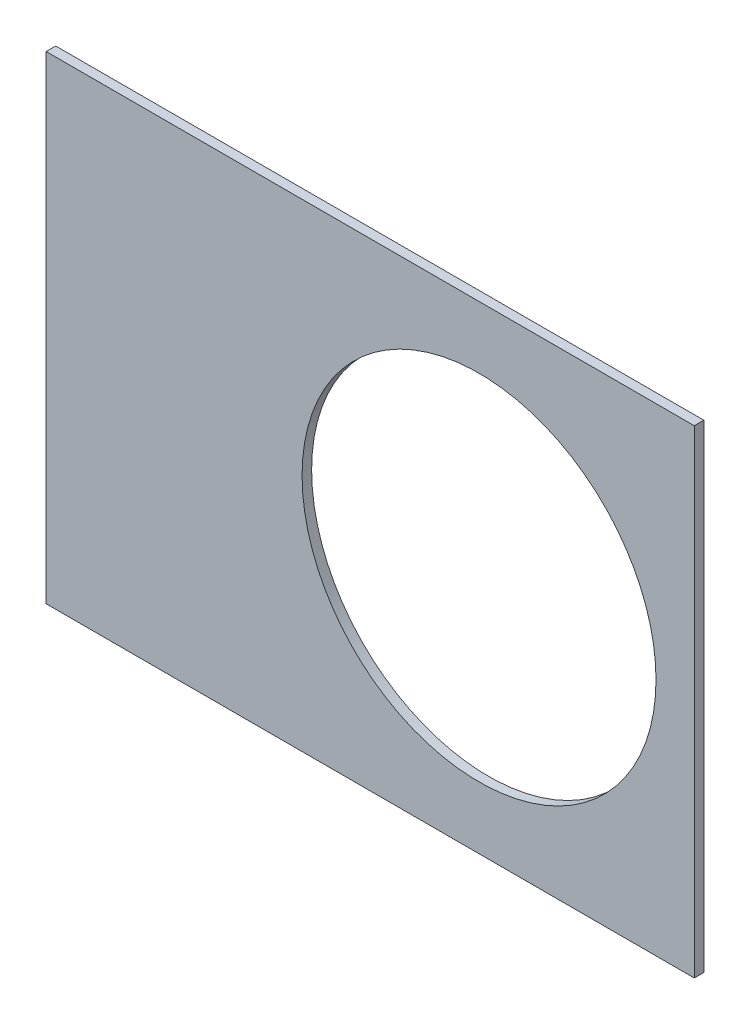
SolidWorks part; units mm, degrees
material "Copper"
ref_plane "Front Plane" through (0, 0, 0) normal (0, 0, 1) x (1, 0, 0)
ref_plane "Top Plane" through (0, 0, 0) normal (0, 1, 0) x (1, 0, 0)
ref_plane "Right Plane" through (0, 0, 0) normal (1, 0, 0) x (0, 0, -1)
sketch "Sketch1" plane through (0, 0, 0) normal (0, 0, 1) x (1, 0, 0)
  line L0 (0, 0) -> (320.3893, 0) construction
  line L1 (0, 0) -> (155.5285, 155.5285) construction
  line L2 (67.2115, 76.1917) -> (8.6967, 17.6769)
  line L3 (8.6967, 17.6769) -> (7.229, 14.1336)
  line L4 (101.4014, -6.35) -> (18.6489, -6.35)
  line L5 (15.1056, -4.8823) -> (18.6489, -6.35)
  line L6 (88.6729, 6.35) -> (27.8605, 6.35)
  line L9 (67.1914, 58.2111) -> (24.1905, 15.2102)
  line L10 (0, 0) -> (40.4486, 97.6516) construction
  line L11 (0, 0) -> (123.4567, -51.1374) construction
  line L18 (8.6967, 17.6769) -> (13.294, 8.6183) construction
  line L19 (18.6489, -6.35) -> (15.4943, 3.3063) construction
  line L20 (27.8605, 6.35) -> (27.7442, 6.7059) construction
  line L21 (24.1905, 15.2102) -> (24.3599, 14.8764) construction
  arc A0 (7.229, 14.1336) -> (15.1056, -4.8823) centre (0, 0) cw
  arc A1 (67.2115, 76.1917) -> (101.4014, -6.35) centre (0, 0) cw
  arc A2 (24.1905, 15.2102) -> (27.8605, 6.35) centre (0, 0) cw
  arc A3 (67.1914, 58.2111) -> (88.6729, 6.35) centre (0, 0) cw
  arc A8 (13.294, 8.6183) -> (15.4943, 3.3063) centre (0, 0) cw construction
  arc A9 (24.3599, 14.8764) -> (27.7442, 6.7059) centre (0, 0) cw construction
  dimension "D1" = 45
  dimension "D3" = 6.35
  dimension "D4" = 15.875
  dimension "D7" = 22.5
  dimension "D8" = 101.6
  dimension "D11" = 12.7
  dimension "D12" = 12.7
  dimension "D2" = 6.35
  dimension "D5" = 67.5
  dimension "D9" = 1.27
  dimension "D10" = 1.27
  dimension "D6" = 12.7
extrude "Boss-Extrude1" add sketch "Sketch1" along normal blind 0.254
sketch "Sketch2" plane through (0, 0, 0.254) normal (0, 0, 1) x (1, 0, 0)
  line L0 (0, 0) -> (101.6, 0) construction
  line L1 (0, 0) -> (71.842, 71.842) construction
  line L3 (0, 0) -> (22.225, 0) construction
  line L4 (0, 0) -> (15.7154, 15.7154) construction
  line L5 (0, 0) -> (95.25, 0) construction
  line L6 (0, 0) -> (92.0044, 24.6525) construction
  arc A0 (101.4014, -6.35) -> (67.2115, 76.1917) centre (0, 0) ccw construction
  circle A1 centre (22.225, 0) radius 4.699
  arc A2 (15.1056, -4.8823) -> (7.229, 14.1336) centre (0, 0) ccw construction
  circle A3 centre (36.195, 0) radius 4.699
  circle A4 centre (61.722, 0) radius 4.699
  circle A5 centre (75.692, 0) radius 4.699
  circle A6 centre (95.25, 0) radius 4.699
  circle A7 centre (15.7154, 15.7154) radius 4.699
  circle A8 centre (25.5937, 25.5937) radius 4.699
  circle A9 centre (43.644, 43.644) radius 4.699
  circle A10 centre (53.5223, 53.5223) radius 4.699
  circle A11 centre (92.0044, 24.6525) radius 4.699
  circle A12 centre (82.4889, 47.625) radius 4.699
  circle A13 centre (67.3519, 67.3519) radius 4.699
  dimension "D3" = 9.398
  dimension "D1" = 45
  dimension "D2" = 6.35
  dimension "D4" = 6.35
  dimension "D5" = 13.97
  dimension "D7" = 13.97
  dimension "D8" = 19.558
  dimension "D9" = 45
  dimension "D10" = 15
  dimension "D11" = 25.527
  dimension "D6" = 2
extrude "Cut-Extrude1" cut sketch "Sketch2" against normal through all
sketch "Sketch3" plane through (0, 0, 0.254) normal (0, 0, 1) x (1, 0, 0)
  line L0 (15.2664, 24.2467) -> (17.0625, 26.0427)
  line L1 (15.2664, 24.2467) -> (15.7154, 23.7977)
  line L2 (17.0625, 26.0427) -> (17.5115, 25.5937)
  line L3 (15.7154, 23.7977) -> (17.5115, 25.5937)
  line L4 (67.2115, 76.1917) -> (8.6967, 17.6769) construction
  line L5 (44.9911, 53.9713) -> (43.195, 52.1753)
  line L6 (44.9911, 53.9713) -> (45.4401, 53.5223)
  line L7 (43.195, 52.1753) -> (43.644, 51.7263)
  line L8 (45.4401, 53.5223) -> (43.644, 51.7263)
  line L9 (27.94, -6.35) -> (30.48, -6.35)
  line L10 (27.94, -6.35) -> (27.94, -5.715)
  line L11 (30.48, -6.35) -> (30.48, -5.715)
  line L12 (27.94, -5.715) -> (30.48, -5.715)
  line L13 (18.6489, -6.35) -> (101.4014, -6.35) construction
  line L14 (67.437, -6.35) -> (69.977, -6.35)
  line L15 (67.437, -6.35) -> (67.437, -5.715)
  line L16 (69.977, -6.35) -> (69.977, -5.715)
  line L17 (67.437, -5.715) -> (69.977, -5.715)
  line L18 (29.2307, 38.211) -> (31.0268, 40.007)
  line L19 (29.2307, 38.211) -> (29.6797, 37.762)
  line L20 (31.0268, 40.007) -> (31.4758, 39.558)
  line L21 (29.6797, 37.762) -> (31.4758, 39.558)
  line L22 (56.845, 65.8253) -> (55.049, 64.0292)
  line L23 (56.845, 65.8253) -> (57.294, 65.3763)
  line L24 (55.049, 64.0292) -> (55.498, 63.5802)
  line L25 (57.294, 65.3763) -> (55.498, 63.5802)
  line L26 (47.6885, -6.35) -> (50.2285, -6.35)
  line L27 (47.6885, -6.35) -> (47.6885, -5.715)
  line L28 (50.2285, -6.35) -> (50.2285, -5.715)
  line L29 (47.6885, -5.715) -> (50.2285, -5.715)
  line L30 (84.201, -6.35) -> (86.741, -6.35)
  line L31 (84.201, -6.35) -> (84.201, -5.715)
  line L32 (86.741, -6.35) -> (86.741, -5.715)
  line L33 (84.201, -5.715) -> (86.741, -5.715)
  line L34 (0, 0) -> (100.7308, 13.2615) construction
  line L35 (0, 0) -> (93.8662, 38.8806) construction
  line L36 (0, 0) -> (80.6047, 61.8502) construction
  line L37 (0, 0) -> (101.6, 0) construction
  line L38 (99.9355, 14.4377) -> (100.267, 11.9194)
  line L39 (99.9355, 14.4377) -> (101.1946, 14.6035)
  line L40 (100.267, 11.9194) -> (101.5261, 12.0852)
  line L41 (101.1946, 14.6035) -> (101.5261, 12.0852)
  line L42 (99.9355, 14.4377) -> (101.5261, 12.0852) construction
  line L43 (100.267, 11.9194) -> (101.1946, 14.6035) construction
  line L44 (93.7655, 37.4643) -> (94.9388, 37.9503)
  line L45 (93.7655, 37.4643) -> (92.7935, 39.811)
  line L46 (94.9388, 37.9503) -> (93.9668, 40.297)
  line L47 (92.7935, 39.811) -> (93.9668, 40.297)
  line L48 (93.7655, 37.4643) -> (93.9668, 40.297) construction
  line L49 (94.9388, 37.9503) -> (92.7935, 39.811) construction
  line L50 (79.3278, 62.4712) -> (80.874, 60.456)
  line L51 (79.3278, 62.4712) -> (80.3354, 63.2443)
  line L52 (80.874, 60.456) -> (81.8816, 61.2292)
  line L53 (80.3354, 63.2443) -> (81.8816, 61.2292)
  line L54 (79.3278, 62.4712) -> (81.8816, 61.2292) construction
  line L55 (80.874, 60.456) -> (80.3354, 63.2443) construction
  line L56 (13.5939, 7.0054) -> (14.5659, 4.6588)
  line L57 (13.5939, 7.0054) -> (14.7672, 7.4914)
  line L58 (14.5659, 4.6588) -> (15.7393, 5.1448)
  line L59 (14.7672, 7.4914) -> (15.7393, 5.1448)
  line L60 (13.5939, 7.0054) -> (15.7393, 5.1448) construction
  line L61 (14.5659, 4.6588) -> (14.7672, 7.4914) construction
  circle A0 centre (15.7154, 15.7154) radius 4.699 construction
  circle A1 centre (43.644, 43.644) radius 4.699 construction
  circle A2 centre (22.225, 0) radius 4.699 construction
  circle A3 centre (61.722, 0) radius 4.699 construction
  arc A4 (101.4014, -6.35) -> (67.2115, 76.1917) centre (0, 0) ccw construction
  arc A9 (15.1056, -4.8823) -> (7.229, 14.1336) centre (0, 0) ccw construction
  circle A10 centre (36.195, 0) radius 4.699 construction
  circle A11 centre (75.692, 0) radius 4.699 construction
  circle A12 centre (25.5937, 25.5937) radius 4.699 construction
  circle A13 centre (53.5223, 53.5223) radius 4.699 construction
  point P75 (14.6666, 6.0751)
  dimension "D2" = 5.715
  dimension "D3" = 2.54
  dimension "D6" = 5.715
  dimension "D8" = 0.635
  dimension "D9" = 5.715
  dimension "D12" = 5.715
  dimension "D4" = 7.5
  dimension "D5" = 22.5
  dimension "D7" = 37.5
  dimension "D10" = 90
  dimension "D11" = 1.27
  dimension "D14" = 0.635
  dimension "D15" = 90
  dimension "D18" = 0.635
  dimension "D19" = 90
  dimension "D22" = 0.635
  dimension "D20" = 1.27
  dimension "D17" = 0.635
  dimension "D13" = 11.4935
  dimension "D16" = 8.509
  dimension "D21" = 11.4935
  dimension "D23" = 8.509
extrude "Cut-Extrude2" cut sketch "Sketch3" against normal through all
sketch "Sketch5" plane through (0, 0, 0.254) normal (0, 0, 1) x (1, 0, 0)
  line L0 (47.6885, -5.715) -> (47.6885, -6.35) construction
  line L1 (50.2285, -7.62) -> (67.437, -7.62)
  line L2 (50.2285, -7.62) -> (50.2285, 7.62)
  line L4 (50.2285, 7.62) -> (67.437, 7.62)
  line L5 (67.437, -7.62) -> (67.437, 7.62)
  line L8 (69.977, -6.35) -> (69.977, -5.715) construction
  line L9 (50.2285, -6.35) -> (67.437, -6.35) construction
  line L10 (27.8605, 6.35) -> (88.6729, 6.35) construction
  dimension "D1" = 2.54
  dimension "D2" = 2.54
  dimension "D3" = 1.27
  dimension "D4" = 1.27
extrude "Cut-Extrude5" cut sketch "Sketch5" against normal through all flip side to cut
equation "\"cSep\"= 1.005"
equation "\"D11@Sketch2\"=\"cSep\""
equation "\"cSep2\"= \"D8@Sketch2\""
equation "\"D13@Sketch3\"=\"cSep\"/2-.05"
equation "\"D16@Sketch3\"=\"cSep2\"/2-.05"
equation "\"D21@Sketch3\"=\"cSep\"/2-.05"
equation "\"D23@Sketch3\"=\"cSep2\"/2-.05"
